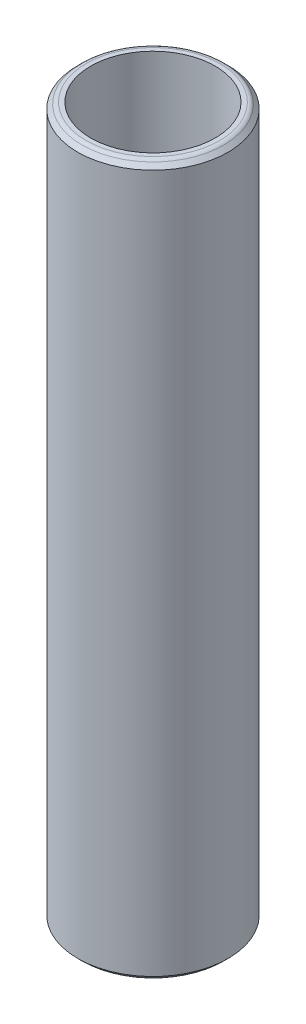
SolidWorks part; units mm, degrees
ref_plane "Front Plane" through (0, 0, 0) normal (0, 0, 1) x (1, 0, 0)
ref_plane "Top Plane" through (0, 0, 0) normal (0, 1, 0) x (1, 0, 0)
ref_plane "Right Plane" through (0, 0, 0) normal (1, 0, 0) x (0, 0, -1)
sketch "Sketch1" plane through (0, 0, 0) normal (0, 1, 0) x (1, 0, 0)
  circle A0 centre (0, 0) radius 3.175
  dimension "D1" = 6.35
extrude "Boss-Extrude2" add sketch "Sketch1" along normal blind 30
chamfer "Chamfer1" distance 0.25 angle 45 1 edges at (0, 30, 3.175)
chamfer "Chamfer2" distance 0.25 angle 45 1 edges at (0, 0, 3.175)
sketch "Sketch10" plane through (0, 0, 0) normal (0, 1, 0) x (1, 0, 0)
  circle A0 centre (0, 0) radius 2.6327
extrude "Cut-Extrude2" cut sketch "Sketch10" along normal blind 34
fillet "Fillet2" radius 0.25 1 edges at (0, 30, 2.925)
fillet "Fillet3" radius 0.25 1 edges at (0, 0, 2.925)
sketch "Sketch13" plane through (0, 0, 0) normal (0, 1, 0) x (1, 0, 0)
  circle A0 centre (0, 0) radius 3.175
curve "Helix/Spiral2" pitch 0.25 height 8.75 turns 35
ref_plane "Plane2" through (0, 30, 0) normal (0, 1, 0) x (1, 0, 0)
sketch "Sketch21" plane through (0, 30, 0) normal (0, 1, 0) x (1, 0, 0)
  circle A0 centre (0, 0) radius 3.175
curve "Helix/Spiral3" pitch 0.25 height 8.75 turns 35
